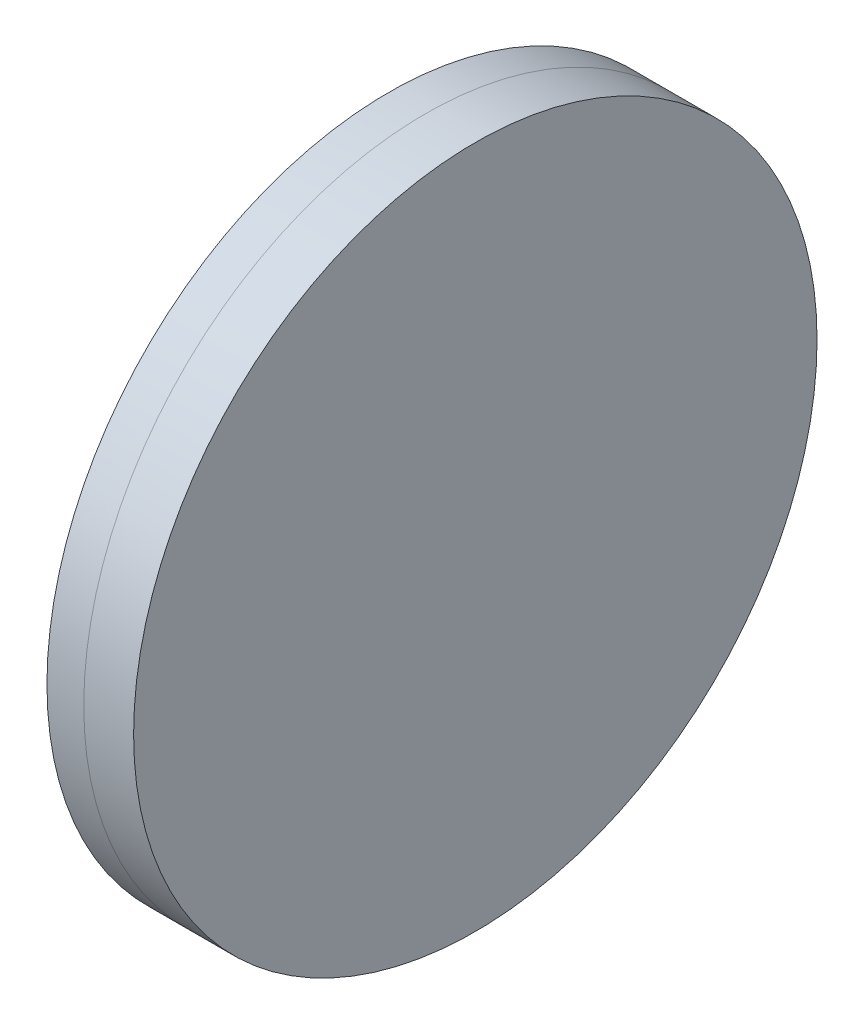
SolidWorks part; units mm, degrees
ref_plane "前视基准面" through (0, 0, 0) normal (0, 0, 1) x (1, 0, 0)
ref_plane "上视基准面" through (0, 0, 0) normal (0, 1, 0) x (1, 0, 0)
ref_plane "右视基准面" through (0, 0, 0) normal (1, 0, 0) x (0, 0, -1)
sketch "草图1" plane through (0, 0, 0) normal (0, 1, 0) x (1, 0, 0)
  line L0 (-402.0213, 0) -> (646.9917, 0) construction
  line L1 (73.2021, -25.4) -> (75.938, -25.4)
  line L2 (73.2021, 25.4) -> (75.938, 25.4)
  arc A0 (75.938, -25.4) -> (75.938, 25.4) centre (-321.3509, 0) ccw
  arc A1 (73.2021, 25.4) -> (73.2021, -25.4) centre (566.8491, 0) ccw
  point P10 (72.5491, 0)
  point P11 (76.7491, 0)
  dimension "D3" = 494.3
  dimension "D4" = 398.1
  dimension "D1" = 25.4
  dimension "D2" = 25.4
  dimension "D5" = 4.2
revolve "旋转1" add sketch "草图1" angle 360 about L0
sketch "草图2" plane through (0, 0, 0) normal (0, 1, 0) x (1, 0, 0)
  line L0 (-151.1285, 0) -> (622.6607, 0) construction
  line L2 (75.938, 25.4) -> (79.6429, 25.4)
  line L3 (75.938, -25.4) -> (79.6429, -25.4)
  arc A0 (79.6429, 25.4) -> (79.6429, -25.4) centre (3519.5491, 0) ccw
  arc A1 (75.938, -25.4) -> (75.938, 25.4) centre (-321.3509, 0) ccw construction
  arc A2 (75.938, -25.4) -> (75.938, 25.4) centre (-321.3509, 0) ccw
  point P4 (76.7491, 0)
  point P8 (79.5491, 0)
  dimension "D1" = 3440
  dimension "D2" = 2.8
revolve "旋转3" add sketch "草图2" angle 360 about L0
